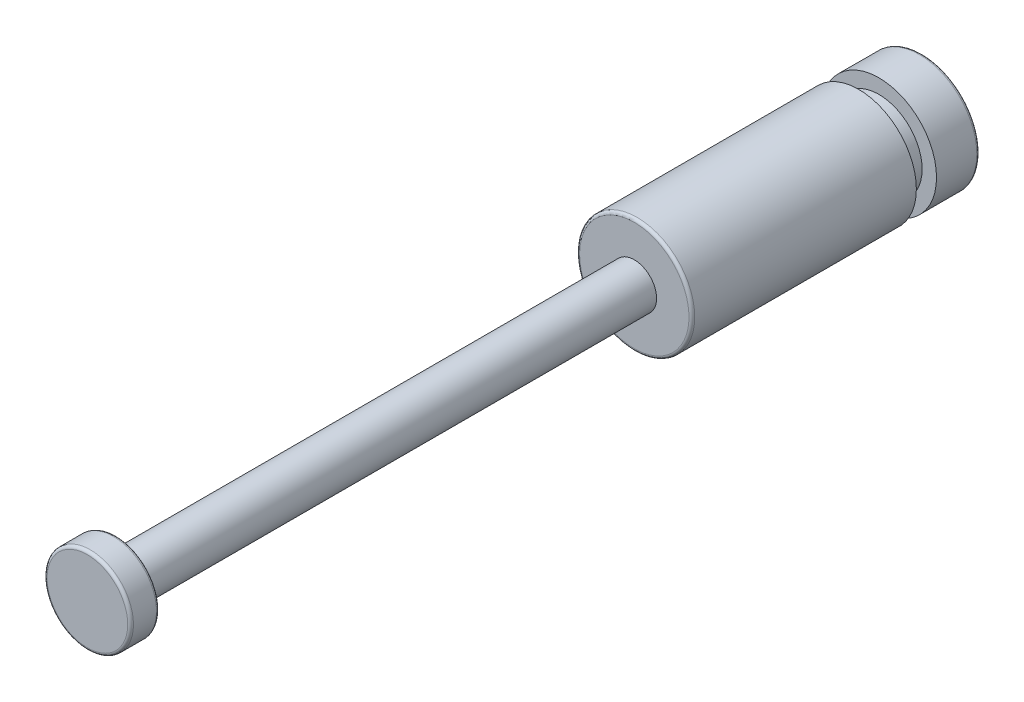
SolidWorks part; units mm, degrees
ref_plane "Front Plane" through (0, 0, 0) normal (0, 0, 1) x (1, 0, 0)
ref_plane "Top Plane" through (0, 0, 0) normal (0, 1, 0) x (1, 0, 0)
ref_plane "Right Plane" through (0, 0, 0) normal (1, 0, 0) x (0, 0, -1)
sketch "Sketch1" plane through (0, 0, 0) normal (0, 0, 1) x (1, 0, 0)
  circle A0 centre (0, 0) radius 0.775
  dimension "D1" = 1.55
extrude "Boss-Extrude1" add sketch "Sketch1" along normal blind 18
sketch "Sketch2" plane through (0, 0, 18) normal (0, 0, 1) x (1, 0, 0)
  circle A0 centre (0, 0) radius 1.5
  dimension "D1" = 3
extrude "Boss-Extrude2" add sketch "Sketch2" along normal blind 1
sketch "Sketch3" plane through (0, 0, 0) normal (0, 0, -1) x (-1, 0, 0)
  circle A0 centre (0, 0) radius 2
  dimension "D1" = 4
extrude "Boss-Extrude4" add sketch "Sketch3" along normal blind 10
sketch "Sketch5" plane through (0, 0, 0) normal (1, 0, 0) x (0, 0, -1)
  line L0 (10, 2) -> (0, 2) construction
  line L1 (7.8, 2) -> (8.5, 2)
  line L2 (7.8, 2) -> (7.8, 1.5)
  line L3 (7.8, 1.5) -> (8.5, 1.5)
  line L4 (8.5, 2) -> (8.5, 1.5)
  line L5 (10, -2) -> (10, 2) construction
  line L6 (0, 0) -> (10, 0) construction
  dimension "D1" = 0.5
  dimension "D2" = 0.7
  dimension "D3" = 1.5
revolve "Cut-Revolve1" cut sketch "Sketch5" angle 360 about L6
fillet "Fillet1" radius 0.1 4 edges at (1.5, 0, 18) (1.5, 0, 19) (-2, 0, 0) (-2, 0, -10)
